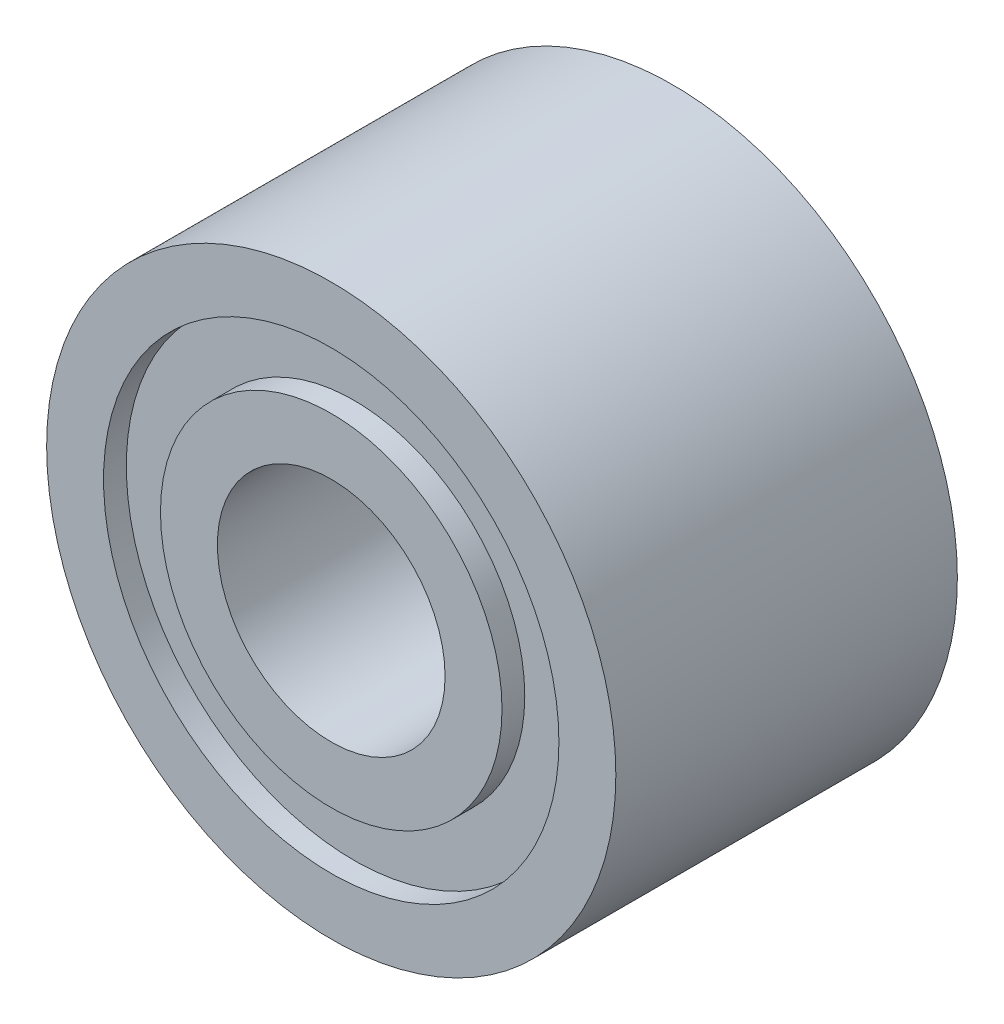
SolidWorks part; units mm, degrees
ref_plane "Front Plane" through (0, 0, 0) normal (0, 0, 1) x (1, 0, 0)
ref_plane "Top Plane" through (0, 0, 0) normal (0, 1, 0) x (1, 0, 0)
ref_plane "Right Plane" through (0, 0, 0) normal (1, 0, 0) x (0, 0, -1)
sketch "Sketch2" plane through (0, 0, 0) normal (1, 0, 0) x (0, 0, -1)
  line L0 (0, 0) -> (4.251, 0) construction
  line L1 (1.1092, 2.5) -> (4.1092, 2.5)
  line L2 (4.1092, 2.5) -> (4.1092, 2)
  line L3 (4.1092, 2) -> (3.9092, 2)
  line L4 (3.9092, 2) -> (3.9092, 1.5)
  line L5 (3.9092, 1.5) -> (4.1092, 1.5)
  line L6 (4.1092, 1.5) -> (4.1092, 1)
  line L7 (4.1092, 1) -> (1.1092, 1)
  line L8 (1.1092, 1) -> (1.1092, 1.5)
  line L9 (1.1092, 1.5) -> (1.3092, 1.5)
  line L10 (1.3092, 1.5) -> (1.3092, 2)
  line L11 (1.3092, 2) -> (1.1092, 2)
  line L12 (1.1092, 2) -> (1.1092, 2.5)
  point P14 (2.6092, 2.5)
  point P16 (2.6092, 1)
  dimension "D1" = 3
  dimension "D2" = 2
  dimension "D3" = 5
  dimension "D4" = 0.5
  dimension "D5" = 0.2
  dimension "D6" = 0.5
revolve "Revolve1" add sketch "Sketch2" angle 360 about L0
